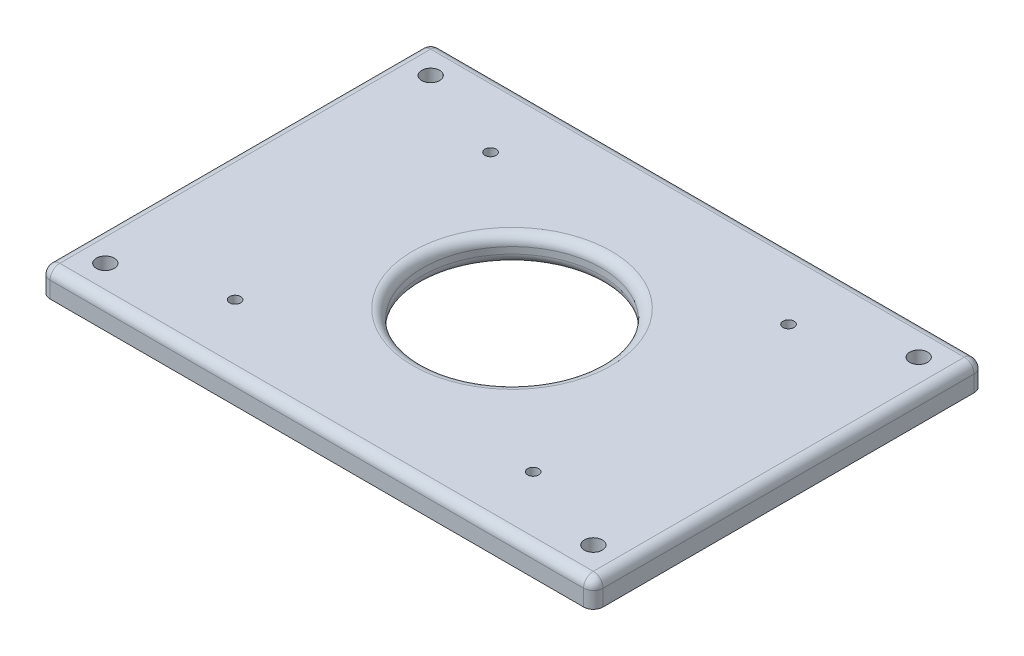
SolidWorks part; units mm, degrees
ref_plane "Front Plane" through (0, 0, 0) normal (0, 0, 1) x (1, 0, 0)
ref_plane "Top Plane" through (0, 0, 0) normal (0, 1, 0) x (1, 0, 0)
ref_plane "Right Plane" through (0, 0, 0) normal (1, 0, 0) x (0, 0, -1)
sketch "Sketch1" plane through (0, 0, 0) normal (0, 0, 1) x (1, 0, 0)
  line L0 (-85, 0) -> (0, 0)
  line L1 (0, 0) -> (85, 0)
  line L2 (85, 0) -> (85, -8)
  line L3 (85, -8) -> (-85, -8)
  line L4 (-85, -8) -> (-85, 0)
  dimension "D1" = 170
  dimension "D2" = 8
extrude "Boss-Extrude1" add sketch "Sketch1" against normal blind 170
sketch "Sketch2" plane through (0, 0, 0) normal (0, 1, 0) x (1, 0, 0)
  line L0 (85, 0) -> (-85, 0) construction
  line L1 (-85, 170) -> (-85, 0) construction
  line L2 (85, 170) -> (85, 0) construction
  line L3 (85, 170) -> (-85, 170) construction
  circle A0 centre (-75, 35) radius 2.75
  circle A1 centre (75, 35) radius 2.75
  circle A2 centre (75, 135) radius 2.75
  circle A3 centre (-75, 135) radius 2.75
  dimension "D1" = 5.5
  dimension "D2" = 5.5
  dimension "D3" = 5.5
  dimension "D4" = 5.5
  dimension "D5" = 35
  dimension "D6" = 10
  dimension "D7" = 35
  dimension "D8" = 10
  dimension "D9" = 35
  dimension "D10" = 10
  dimension "D11" = 35
  dimension "D12" = 10
extrude "Cut-Extrude1" cut sketch "Sketch2" against normal through all
sketch "Sketch3" plane through (0, 0, 0) normal (0, 1, 0) x (1, 0, 0)
  line L0 (85, 0) -> (-85, 0) construction
  line L2 (85, 170) -> (85, 0) construction
  circle A0 centre (-45.35, 45.25) radius 1.7
  circle A1 centre (46.25, 45.25) radius 1.7
  circle A2 centre (46.25, 123.75) radius 1.7
  circle A3 centre (-45.35, 123.75) radius 1.7
  dimension "D1" = 3.4
  dimension "D2" = 3.4
  dimension "D3" = 3.4
  dimension "D4" = 3.4
  dimension "D5" = 91.6
  dimension "D6" = 91.6
  dimension "D7" = 78.5
  dimension "D8" = 78.5
  dimension "D9" = 45.25
  dimension "D10" = 38.75
extrude "Cut-Extrude2" cut sketch "Sketch3" against normal through all
sketch "Sketch4" plane through (0, -8, 0) normal (0, -1, 0) x (1, 0, 0)
  circle A0 centre (-45.35, -45.25) radius 3.375
  circle A1 centre (46.25, -45.25) radius 3.375
  circle A2 centre (46.25, -123.75) radius 3.375
  circle A3 centre (-45.35, -123.75) radius 3.375
  dimension "D1" = 6.75
  dimension "D2" = 6.75
  dimension "D3" = 6.75
  dimension "D4" = 6.75
extrude "Cut-Extrude3" cut sketch "Sketch4" against normal blind 3.5
fillet "Fillet1" radius 3 4 edges at (0, 0, -170) (0, 0, 0) (-85, 0, -85) (85, 0, -85)
sketch "Sketch5" plane through (0, 0, 0) normal (0, 1, 0) x (1, 0, 0)
  line L0 (-82, 3) -> (82, 3) construction
  circle A0 centre (-0.5, 85.5) radius 27.5
  point P3 (0, 0)
  dimension "D1" = 55
  dimension "D2" = 82.5
  dimension "D3" = 82.5
extrude "Cut-Extrude4" cut sketch "Sketch5" against normal through all
fillet "Fillet2" radius 3 1 edges at (-0.5, 0, -58)
fillet "Fillet3" radius 3 1 edges at (-0.5, -8, -58)
sketch "Sketch6" plane through (0, 0, 0) normal (0, 1, 0) x (1, 0, 0)
  line L0 (-85, 170) -> (85, 170)
  line L1 (85, 170) -> (85, 145)
  line L2 (85, 170) -> (85, 0) construction
  line L3 (85, 145) -> (-85, 145)
  line L4 (-85, 0) -> (-85, 170) construction
  line L5 (-85, 145) -> (-85, 170)
  line L6 (-85, 0) -> (85, 0)
  line L7 (85, 0) -> (85, 25)
  line L8 (85, 25) -> (-85, 25)
  line L9 (-85, 25) -> (-85, 0)
  dimension "D1" = 25
  dimension "D2" = 25
extrude "Cut-Extrude5" cut sketch "Sketch6" against normal through all
fillet "Fillet4" radius 3 5 edges at (0, 0, -145) (-84.1213, -0.8787, -145) (84.1213, -0.8787, -145) (-85, -5.5, -145) (85, -5.5, -145)
fillet "Fillet5" radius 3 5 edges at (-84.1213, -0.8787, -25) (84.1213, -0.8787, -25) (85, -5.5, -25) (-85, -5.5, -25) (0, 0, -25)
